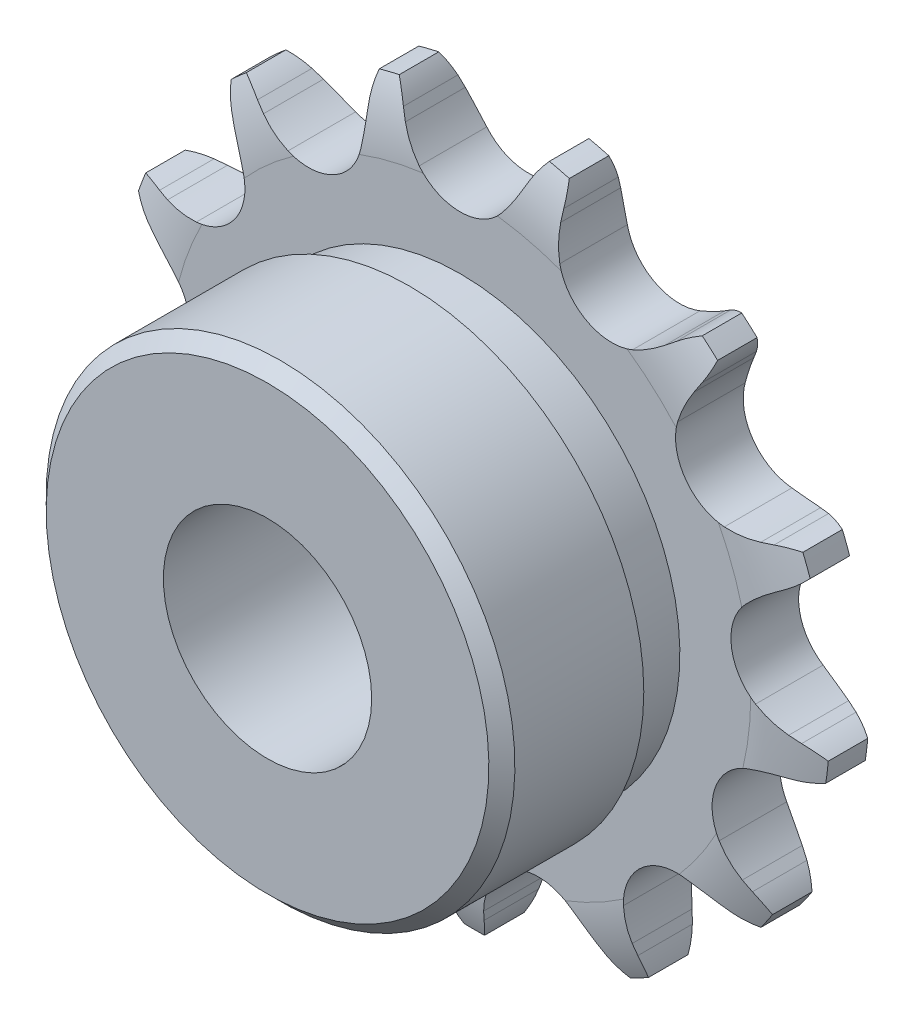
SolidWorks part; units mm, degrees
ref_plane "Front Plane" through (0, 0, 0) normal (0, 0, 1) x (1, 0, 0)
ref_plane "Top Plane" through (0, 0, 0) normal (0, 1, 0) x (1, 0, 0)
ref_plane "Right Plane" through (0, 0, 0) normal (1, 0, 0) x (0, 0, -1)
sketch "Sketch0" plane through (0, 0, 0) normal (0, 0, 1) x (1, 0, 0)
  line L0 (3, -12.1715) -> (0, 0) construction
  line L1 (0, 0) -> (8.3127, -9.3831) construction
  line L2 (0, 0) -> (-3, -12.1715) construction
  line L3 (3, -12.1715) -> (8.3127, -9.3831) construction
  line L4 (3, -12.1715) -> (-3, -12.1715) construction
  line L5 (5.3936, -11.7037) -> (5.1287, -11.3853)
  line L6 (3, -12.1715) -> (0, -12.9109) construction
  line L7 (0.6632, -12.8697) -> (0.7498, -12.4646)
  line L8 (0, -12.1715) -> (0, -13.9715) construction
  line L9 (4.2194, -10.5259) -> (1.0948, -14.7425) construction
  line L10 (0, 0) -> (0, -12.1715) construction
  line L11 (5.1287, -11.3853) -> (1.0948, -14.7425) construction
  line L12 (0, -13.9715) -> (0, -14.2633) construction
  line L13 (7.9586, -9.569) -> (5.3936, -11.7037) construction
  circle A0 centre (0, 0) radius 13.9715 construction
  circle A1 centre (0, 0) radius 12.5357 construction
  arc A2 (-3.2971, -15.4349) -> (10.0924, -12.1347) centre (0, 0) ccw
  circle A3 centre (0, 0) radius 14.2633 construction
  circle A4 centre (3, -12.1715) radius 2 construction
  arc A7 (4.2194, -10.5259) -> (1.1556, -11.2811) centre (3, -12.1715) ccw
  circle A8 centre (3, -12.1715) radius 2.0481 construction
  arc A9 (5.3936, -11.7037) -> (10.0924, -12.1347) centre (7.9586, -9.569) ccw
  arc A10 (5.1287, -11.3853) -> (4.2194, -10.5259) centre (1.0948, -14.7425) ccw
  arc A11 (0.6632, -12.8697) -> (-3.2971, -15.4349) centre (-2.6, -12.1715) cw
  arc A12 (0.7498, -12.4646) -> (1.1556, -11.2811) centre (5.8818, -13.5627) cw
  dimension "D1" = 2.0481
  dimension "R" = 2.0481
sketch "Sketch1" plane through (0, 0, 0) normal (1, 0, 0) x (0, 0, -1)
  line L0 (1.3, 0) -> (-1.3, 0)
  line L1 (-1.3, 0) -> (-1.3, 11.159)
  line L2 (-1.3, 12.5357) -> (0, 12.5357) construction
  line L3 (-0.6, 13.9715) -> (0.6, 13.9715)
  line L5 (1.3, 11.159) -> (1.3, 0)
  line L7 (0, 13.9715) -> (0, 0) construction
  line L8 (-1.3, 11.159) -> (1.3, 11.159) construction
  line L9 (0, 13.9715) -> (0, -13.9715) construction
  line L10 (-1.3, 11.159) -> (-1.3, 13.9715) construction
  line L11 (-1.3, 13.9715) -> (-0.6, 13.9715) construction
  line L12 (0.6, 13.9715) -> (1.3, 13.9715) construction
  line L13 (1.3, 13.9715) -> (1.3, 11.159) construction
  line L14 (0, 0) -> (-6.4008, 0) construction
  line L15 (-1.3, 12.5357) -> (-1.3, 8.4357) construction
  line L22 (1.3, 0) -> (-8.7, 0) construction
  line L24 (-1.3, 0) -> (-1.3, 8.4357) construction
  arc A0 (-0.6, 13.9715) -> (-1.3, 11.159) centre (4.7, 11.159) ccw
  arc A1 (0.6, 13.9715) -> (1.3, 11.159) centre (-4.7, 11.159) cw
  dimension "R" = 6
revolve "Revolve1" add sketch "Sketch1" angle 360 mid plane about L0
extrude "Cut-Extrude1" cut sketch "Sketch0" against normal through all and the other way through all
pattern_circular "CirPattern1" count 13 over 360 about axis through (0, 0, 0) along (0, 0, 1) of "Cut-Extrude1"
sketch "Sketch2" plane through (0, 0, 0) normal (0, 0, 1) x (1, 0, 0)
  circle A0 centre (0, 0) radius 4 construction
  circle A1 centre (0, 0) radius 9
  circle A2 centre (0, 0) radius 13.65 construction
  dimension "Bore" = 8
  dimension "Hub Dia." = 18
  dimension "OD" = 27.3
extrude "Boss-Extrude1" add sketch "Sketch2" along normal up to vertex (8.7 mm away) from surface at 1.3 starting at face at (0, 0, 1.3)
sketch "Sketch3" plane through (0, 0, 0) normal (0, 0, 1) x (1, 0, 0)
  circle A0 centre (0, 0) radius 4 construction
  circle A1 centre (0, 0) radius 4
extrude "Cut-Extrude2" cut sketch "Sketch3" along normal through all and the other way through all
sketch "Sketch4" plane through (0, 0, 0) normal (1, 0, 0) x (0, 0, -1)
  line L0 (-8.7, 9) -> (-8.7, 8.5)
  line L1 (-1.3, 13.9715) -> (-3.25, 13.9715)
  line L2 (-1.3, 13.9715) -> (-1.3, 8.4357)
  line L3 (-1.3, 8.4357) -> (-3.25, 8.4357)
  line L4 (-3.25, 13.9715) -> (-3.25, 8.4357)
  line L9 (-8.7, 8.5) -> (-8.2, 9)
  line L10 (-8.2, 9) -> (-8.7, 9)
  dimension "C" = 0.5
  dimension "D3" = 1.95
revolve "Cut-Revolve1" cut sketch "Sketch4" angle 360 mid plane about L22
sketch "Sketch5" plane through (0, 0, 0) normal (0, 0, 1) x (1, 0, 0)
  circle A0 centre (0, 0) radius 13.65 construction
  circle A1 centre (0, 0) radius 13.65
extrude "Cut-Extrude3" cut sketch "Sketch5" against normal through all and the other way through all flip side to cut
equation "\"360/N@Sketch0\" = 360/\"Teeth@CirPattern1\""
equation "\"Ds@Sketch0\" = 1.005 * \"Dr@Sketch0\" + ( 0.003 * 25.4 ) "
equation "\"R@Sketch0\" = 1/2 * \"Ds@Sketch0\""
equation "\"A@Sketch0\" = 35 +  ( 60 / \"Teeth@CirPattern1\" ) "
equation "\"B@Sketch0\" = 18 -  ( 56 / \"Teeth@CirPattern1\" )"
equation "\"ac@Sketch0\" = 0.8 * \"Dr@Sketch0\""
equation "\"ab@Sketch0\" = 1.4 * \"Dr@Sketch0\""
equation "\"J@Sketch0\" = 0.3 * \"Pitch@Sketch0\""
equation "\"D3@Sketch4\" = \"t@Sketch1\" * 3 / 4"
